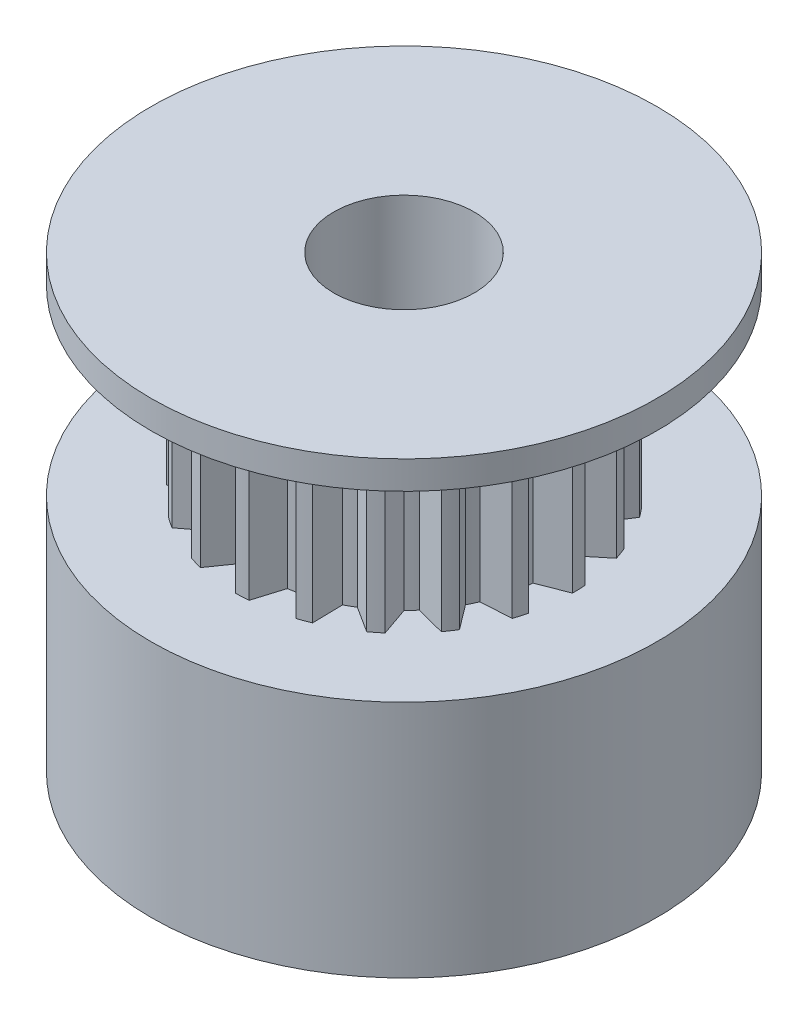
SolidWorks part; units mm, degrees
ref_plane "前视基准面" through (0, 0, 0) normal (0, 0, 1) x (1, 0, 0)
ref_plane "上视基准面" through (0, 0, 0) normal (0, 1, 0) x (1, 0, 0)
ref_plane "右视基准面" through (0, 0, 0) normal (1, 0, 0) x (0, 0, -1)
sketch "草图1" plane through (0, 0, 0) normal (0, 1, 0) x (1, 0, 0)
  circle A0 centre (0, 0) radius 9
  dimension "D1" = 18
extrude "凸台-拉伸1" add sketch "草图1" along normal blind 8.5
sketch "草图2" plane through (0, 8.5, 0) normal (0, 1, 0) x (1, 0, 0)
  circle A0 centre (0, 0) radius 6
  dimension "D1" = 12
extrude "凸台-拉伸2" add sketch "草图2" along normal blind 6.5
sketch "草图3" plane through (0, 15, 0) normal (0, 1, 0) x (1, 0, 0)
  circle A0 centre (0, 0) radius 9
  dimension "D1" = 18
extrude "凸台-拉伸3" add sketch "草图3" along normal blind 1
sketch "草图4" plane through (0, 16, 0) normal (0, 1, 0) x (1, 0, 0)
  circle A0 centre (0, 0) radius 2.5
  dimension "D1" = 5
extrude "切除-拉伸1" cut sketch "草图4" against normal through all
sketch "草图5" plane through (0, 8.5, 0) normal (0, 1, 0) x (1, 0, 0)
  line L60 (-6, 0) -> (-4.9841, 0.3986)
  line L61 (-5.9819, -0.4662) -> (-4.9382, -0.7837)
  line L82 (-5.8331, 1.4052) -> (-4.9387, 0.7807)
  line L83 (-5.7063, 1.8541) -> (-4.617, 1.9192)
  line L84 (-5.1134, 3.1389) -> (-4.4557, 2.2686)
  line L85 (-4.8541, 3.5267) -> (-3.7979, 3.252)
  line L86 (-3.8932, 4.5654) -> (-3.5366, 3.5345)
  line L87 (-3.5267, 4.8541) -> (-2.6071, 4.2665)
  line L88 (-2.2918, 5.545) -> (-2.2713, 4.4543)
  line L89 (-1.8541, 5.7063) -> (-1.1611, 4.8633)
  line L90 (-0.4662, 5.9819) -> (-0.7837, 4.9382)
  line L91 (0, 6) -> (0.3986, 4.9841)
  line L92 (1.4052, 5.8331) -> (0.7807, 4.9387)
  line L93 (1.8541, 5.7063) -> (1.9192, 4.617)
  line L94 (3.1389, 5.1134) -> (2.2686, 4.4557)
  line L95 (3.5267, 4.8541) -> (3.252, 3.7979)
  line L96 (4.5654, 3.8932) -> (3.5345, 3.5366)
  line L97 (4.8541, 3.5267) -> (4.2665, 2.6071)
  line L98 (5.545, 2.2918) -> (4.4543, 2.2713)
  line L99 (5.7063, 1.8541) -> (4.8633, 1.1611)
  line L100 (5.9819, 0.4662) -> (4.9382, 0.7837)
  line L101 (6, 0) -> (4.9841, -0.3986)
  line L102 (5.8331, -1.4052) -> (4.9387, -0.7807)
  line L103 (5.7063, -1.8541) -> (4.617, -1.9192)
  line L104 (5.1134, -3.1389) -> (4.4557, -2.2686)
  line L105 (4.8541, -3.5267) -> (3.7979, -3.252)
  line L106 (3.8932, -4.5654) -> (3.5366, -3.5345)
  line L107 (3.5267, -4.8541) -> (2.6071, -4.2665)
  line L108 (2.2918, -5.545) -> (2.2713, -4.4543)
  line L109 (1.8541, -5.7063) -> (1.1611, -4.8633)
  line L110 (0.4662, -5.9819) -> (0.7837, -4.9382)
  line L111 (0, -6) -> (-0.3986, -4.9841)
  line L112 (-1.4052, -5.8331) -> (-0.7807, -4.9387)
  line L113 (-1.8541, -5.7063) -> (-1.9192, -4.617)
  line L114 (-3.1389, -5.1134) -> (-2.2686, -4.4557)
  line L115 (-3.5267, -4.8541) -> (-3.252, -3.7979)
  line L116 (-4.5654, -3.8932) -> (-3.5345, -3.5366)
  line L117 (-4.8541, -3.5267) -> (-4.2665, -2.6071)
  line L118 (-5.545, -2.2918) -> (-4.4543, -2.2713)
  line L119 (-5.7063, -1.8541) -> (-4.8633, -1.1611)
  arc A2 (-4.9382, -0.7837) -> (-4.8633, -1.1611) centre (0, 0) ccw
  arc A3 (-5.9819, -0.4662) -> (-5.7063, -1.8541) centre (0, 0) ccw
  arc A4 (-4.9387, 0.7807) -> (-4.9841, 0.3986) centre (0, 0) ccw
  arc A5 (-4.4557, 2.2686) -> (-4.617, 1.9192) centre (0, 0) ccw
  arc A6 (-3.5366, 3.5345) -> (-3.7979, 3.252) centre (0, 0) ccw
  arc A7 (-2.2713, 4.4543) -> (-2.6071, 4.2665) centre (0, 0) ccw
  arc A8 (-0.7837, 4.9382) -> (-1.1611, 4.8633) centre (0, 0) ccw
  arc A9 (0.7807, 4.9387) -> (0.3986, 4.9841) centre (0, 0) ccw
  arc A10 (2.2686, 4.4557) -> (1.9192, 4.617) centre (0, 0) ccw
  arc A11 (3.5345, 3.5366) -> (3.252, 3.7979) centre (0, 0) ccw
  arc A12 (4.4543, 2.2713) -> (4.2665, 2.6071) centre (0, 0) ccw
  arc A13 (4.9382, 0.7837) -> (4.8633, 1.1611) centre (0, 0) ccw
  arc A14 (4.9387, -0.7807) -> (4.9841, -0.3986) centre (0, 0) ccw
  arc A15 (4.4557, -2.2686) -> (4.617, -1.9192) centre (0, 0) ccw
  arc A16 (3.5366, -3.5345) -> (3.7979, -3.252) centre (0, 0) ccw
  arc A17 (2.2713, -4.4543) -> (2.6071, -4.2665) centre (0, 0) ccw
  arc A18 (0.7837, -4.9382) -> (1.1611, -4.8633) centre (0, 0) ccw
  arc A19 (-0.7807, -4.9387) -> (-0.3986, -4.9841) centre (0, 0) ccw
  arc A20 (-2.2686, -4.4557) -> (-1.9192, -4.617) centre (0, 0) ccw
  arc A21 (-3.5345, -3.5366) -> (-3.252, -3.7979) centre (0, 0) ccw
  arc A22 (-4.4543, -2.2713) -> (-4.2665, -2.6071) centre (0, 0) ccw
  arc A23 (-5.8331, 1.4052) -> (-6, 0) centre (0, 0) ccw
  arc A24 (-5.1134, 3.1389) -> (-5.7063, 1.8541) centre (0, 0) ccw
  arc A25 (-3.8932, 4.5654) -> (-4.8541, 3.5267) centre (0, 0) ccw
  arc A26 (-2.2918, 5.545) -> (-3.5267, 4.8541) centre (0, 0) ccw
  arc A27 (-0.4662, 5.9819) -> (-1.8541, 5.7063) centre (0, 0) ccw
  arc A28 (1.4052, 5.8331) -> (0, 6) centre (0, 0) ccw
  arc A29 (3.1389, 5.1134) -> (1.8541, 5.7063) centre (0, 0) ccw
  arc A30 (4.5654, 3.8932) -> (3.5267, 4.8541) centre (0, 0) ccw
  arc A31 (5.545, 2.2918) -> (4.8541, 3.5267) centre (0, 0) ccw
  arc A32 (5.9819, 0.4662) -> (5.7063, 1.8541) centre (0, 0) ccw
  arc A33 (5.8331, -1.4052) -> (6, 0) centre (0, 0) ccw
  arc A34 (5.1134, -3.1389) -> (5.7063, -1.8541) centre (0, 0) ccw
  arc A35 (3.8932, -4.5654) -> (4.8541, -3.5267) centre (0, 0) ccw
  arc A36 (2.2918, -5.545) -> (3.5267, -4.8541) centre (0, 0) ccw
  arc A37 (0.4662, -5.9819) -> (1.8541, -5.7063) centre (0, 0) ccw
  arc A38 (-1.4052, -5.8331) -> (0, -6) centre (0, 0) ccw
  arc A39 (-3.1389, -5.1134) -> (-1.8541, -5.7063) centre (0, 0) ccw
  arc A40 (-4.5654, -3.8932) -> (-3.5267, -4.8541) centre (0, 0) ccw
  arc A41 (-5.545, -2.2918) -> (-4.8541, -3.5267) centre (0, 0) ccw
  point P30 (0, 0)
  point P171 (0, 0)
  dimension "D1" = 10
  dimension "D2" = 6
  dimension "D3" = 20
extrude "切除-拉伸2" cut sketch "草图5" along normal blind 6.5
